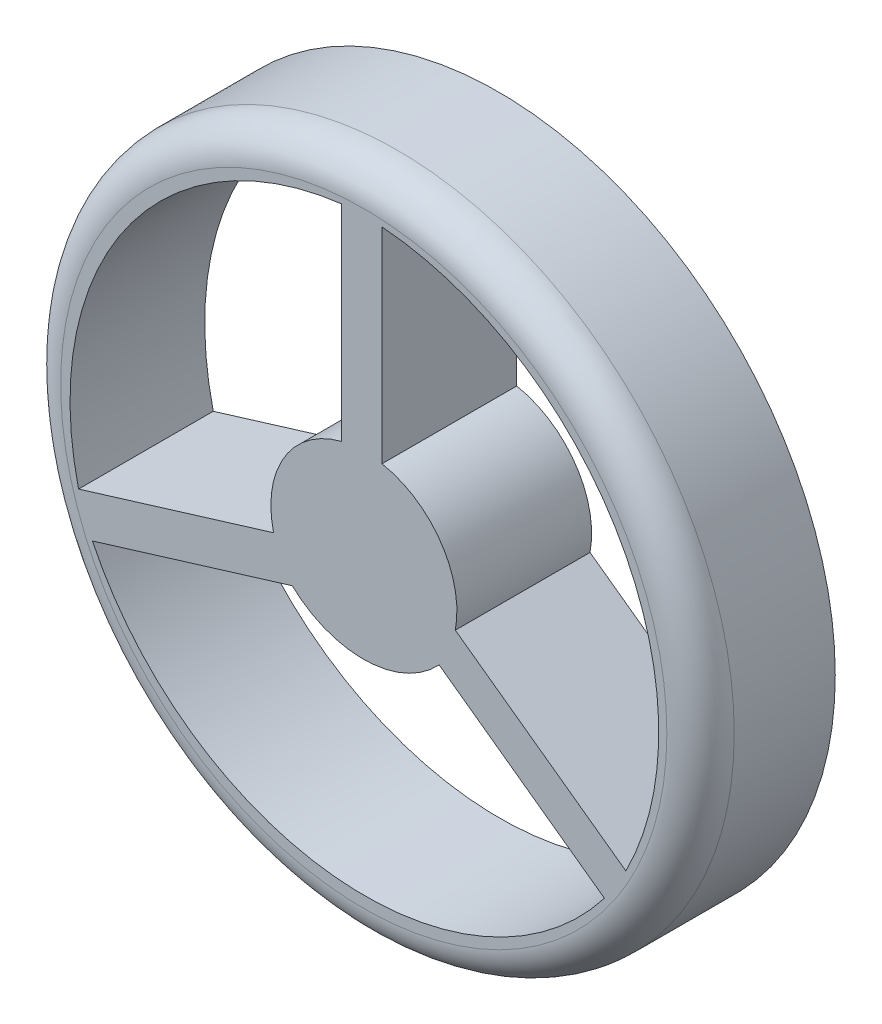
SolidWorks part; units mm, degrees
ref_plane "Front Plane" through (0, 0, 0) normal (0, 0, 1) x (1, 0, 0)
ref_plane "Top Plane" through (0, 0, 0) normal (0, 1, 0) x (1, 0, 0)
ref_plane "Right Plane" through (0, 0, 0) normal (1, 0, 0) x (0, 0, -1)
sketch "Sketch1" plane through (0, 0, 0) normal (0, 0, 1) x (1, 0, 0)
  line L0 (69.0427, 207.1282) -> (345.2136, 207.1282) construction
  circle A6 centre (0, 0) radius 2.54
  dimension "D1" = 5.08
extrude "Boss-Extrude3" add sketch "Sketch1" along normal blind 1.016
fillet "Fillet1" radius 0.254 1 edges at (2.54, 0, 1.016)
sketch "Sketch3" plane through (0, 0, 1.016) normal (0, 0, 1) x (1, 0, 0)
  line L0 (-2.1511, -0.6216) -> (-0.68, -0.1716)
  line L1 (-2.0465, -0.9084) -> (-0.54, -0.4475)
  line L2 (1.8149, -1.3114) -> (0.5684, -0.4107)
  line L3 (0.6904, -0.1228) -> (1.9765, -1.0521)
  line L4 (-0.1674, 0.681) -> (-0.1674, 2.2328)
  line L5 (0.1374, 0.6877) -> (0.1374, 2.2349)
  arc A2 (-2.1511, -0.6216) -> (-0.1674, 2.2328) centre (0.1117, -0.0777) cw
  arc A3 (0.1374, 2.2349) -> (1.9765, -1.0521) centre (-0.0386, -0.0216) cw
  arc A4 (1.8149, -1.3114) -> (-2.0465, -0.9084) centre (0.0086, 0.082) cw
  arc A5 (0.1374, 0.6877) -> (0.6904, -0.1228) centre (0.0086, 0.0059) cw
  arc A6 (-0.68, -0.1716) -> (-0.1674, 0.681) centre (0.0026, -0.0016) cw
  arc A7 (0.5684, -0.4107) -> (-0.54, -0.4475) centre (-0.0041, 0.1251) cw
  dimension "D1" = 0.3048
  dimension "D2" = 0.3048
  dimension "D3" = 0.3048
extrude "Cut-Extrude1" cut sketch "Sketch3" against normal blind 11.176
